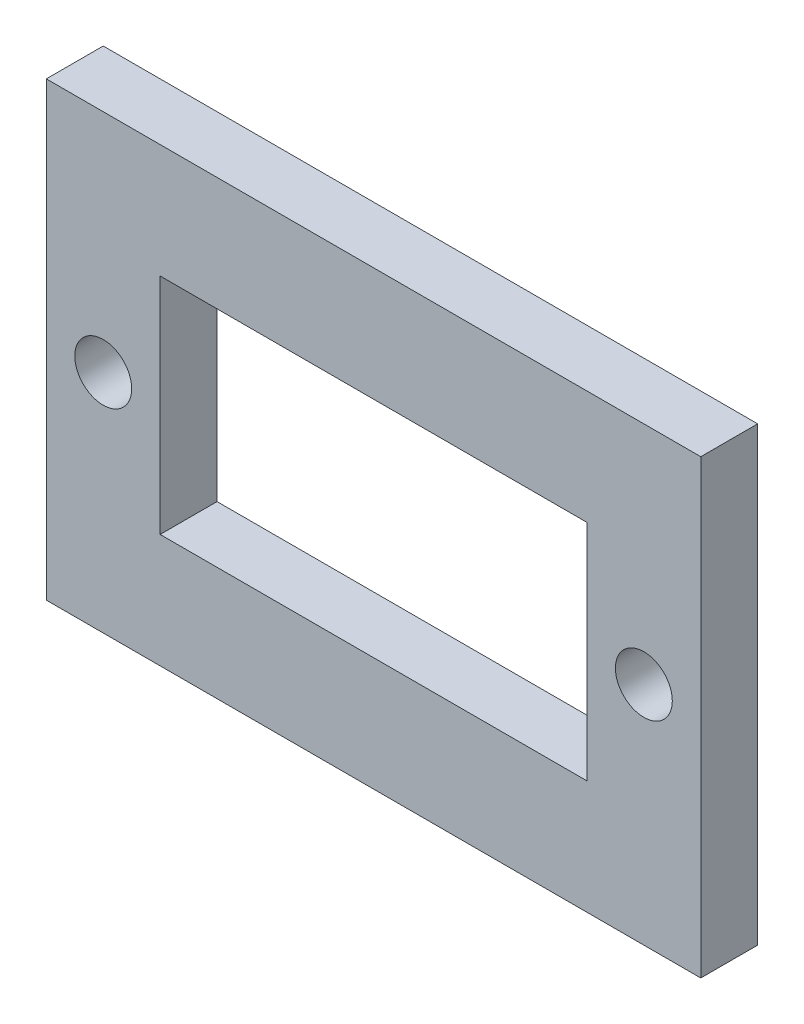
SolidWorks part; units mm, degrees
ref_plane "Front Plane" through (0, 0, 0) normal (0, 0, 1) x (1, 0, 0)
ref_plane "Top Plane" through (0, 0, 0) normal (0, 1, 0) x (1, 0, 0)
ref_plane "Right Plane" through (0, 0, 0) normal (1, 0, 0) x (0, 0, -1)
sketch "Sketch1" plane through (0, 0, 0) normal (0, 0, 1) x (1, 0, 0)
  line L1 (0, 0) -> (22.5, 0)
  line L2 (0, 0) -> (0, 11.8)
  line L3 (0, 11.8) -> (22.5, 11.8)
  line L4 (22.5, 0) -> (22.5, 11.8)
  line L5 (-6, 17.8) -> (28.5, 17.8)
  line L6 (-6, 17.8) -> (-6, -6)
  line L7 (-6, -6) -> (28.5, -6)
  line L8 (28.5, 17.8) -> (28.5, -6)
  line L9 (-6, 17.8) -> (28.5, -6) construction
  line L10 (-6, -6) -> (28.5, 17.8) construction
  circle A0 centre (-3, 5.9) radius 1.5
  circle A1 centre (25.5, 5.9) radius 1.5
  point P5 (11.25, 5.9)
  dimension "D7" = 3
  dimension "D8" = 14.25
  dimension "3" = 3
  dimension "D1" = 11.8
  dimension "D2" = 22.5
  dimension "D3" = 6
  dimension "D4" = 6
  dimension "D5" = 23.8
  dimension "D6" = 34.5
  dimension "D9" = 14.25
  dimension "D10" = 11.9
  dimension "D11" = 11.9
extrude "Boss-Extrude1" add sketch "Sketch1" along normal blind 3
